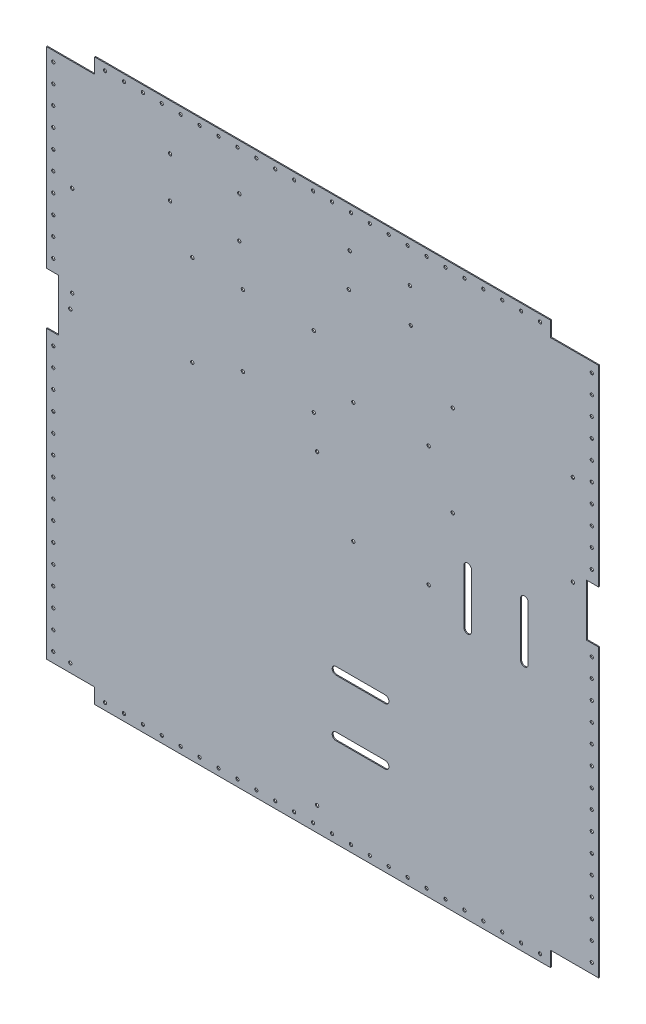
SolidWorks part; units mm, degrees
material "6061-T6 (SS)"
ref_plane "Front Plane" through (0, 0, 0) normal (0, 0, 1) x (1, 0, 0)
ref_plane "Top Plane" through (0, 0, 0) normal (0, 1, 0) x (1, 0, 0)
ref_plane "Right Plane" through (0, 0, 0) normal (1, 0, 0) x (0, 0, -1)
sketch "Sketch1" plane through (0, 0, 0) normal (0, 0, 1) x (1, 0, 0)
  line L0 (0, 374) -> (0, 577)
  line L1 (51, 0) -> (533, 0)
  line L2 (0, 16) -> (0, 319)
  line L3 (51, 593) -> (533, 593)
  line L4 (584, 16) -> (584, 319)
  line L7 (0, 16) -> (51, 16)
  line L8 (51, 0) -> (51, 16)
  line L11 (584, 16) -> (533, 16)
  line L12 (533, 0) -> (533, 16)
  line L13 (0, 319) -> (13, 319)
  line L15 (0, 374) -> (13, 374)
  line L16 (13, 319) -> (13, 374)
  line L17 (584, 319) -> (571, 319)
  line L19 (584, 374) -> (571, 374)
  line L20 (571, 319) -> (571, 374)
  line L23 (0, 577) -> (51, 577)
  line L24 (51, 593) -> (51, 577)
  line L27 (584, 577) -> (533, 577)
  line L28 (533, 593) -> (533, 577)
  line L29 (584, 374) -> (584, 577)
  point P25 (6.5, 319)
  point P26 (25.5, 577)
  dimension "D2" = 593
  dimension "D3" = 16
  dimension "D4" = 584
  dimension "D7" = 13
  dimension "D8" = 319
  dimension "D9" = 219
  dimension "D10" = 16
  dimension "D11" = 51
extrude "Boss-Extrude1" add sketch "Sketch1" along normal blind 1.016 contours L3 L28 L27 L29 L19 L20 L17 L4 L11 L12 L1 L8 L7 L2 L13 L16 L15 L0 L23 L24
sketch "Sketch2" plane through (0, 0, 1.016) normal (0, 0, 1) x (1, 0, 0)
  circle A0 centre (62, 585.825) radius 1.675
  circle A1 centre (82, 585.825) radius 1.675
  circle A2 centre (102, 585.825) radius 1.675
  circle A3 centre (122, 585.825) radius 1.675
  circle A4 centre (142, 585.825) radius 1.675
  circle A5 centre (162, 585.825) radius 1.675
  circle A6 centre (182, 585.825) radius 1.675
  circle A7 centre (202, 585.825) radius 1.675
  circle A8 centre (222, 585.825) radius 1.675
  circle A9 centre (242, 585.825) radius 1.675
  circle A10 centre (262, 585.825) radius 1.675
  circle A11 centre (282, 585.825) radius 1.675
  circle A12 centre (302, 585.825) radius 1.675
  circle A13 centre (322, 585.825) radius 1.675
  circle A14 centre (342, 585.825) radius 1.675
  circle A15 centre (362, 585.825) radius 1.675
  circle A16 centre (382, 585.825) radius 1.675
  circle A17 centre (402, 585.825) radius 1.675
  circle A18 centre (422, 585.825) radius 1.675
  circle A19 centre (442, 585.825) radius 1.675
  circle A20 centre (462, 585.825) radius 1.675
  circle A21 centre (482, 585.825) radius 1.675
  circle A22 centre (502, 585.825) radius 1.675
  circle A23 centre (522, 585.825) radius 1.675
  circle A24 centre (576.725, 566.5) radius 1.675
  circle A25 centre (576.725, 546.5) radius 1.675
  circle A26 centre (576.725, 526.5) radius 1.675
  circle A27 centre (576.725, 506.5) radius 1.675
  circle A28 centre (576.725, 486.5) radius 1.675
  circle A29 centre (576.725, 466.5) radius 1.675
  circle A30 centre (576.725, 446.5) radius 1.675
  circle A31 centre (576.725, 426.5) radius 1.675
  circle A32 centre (576.725, 406.5) radius 1.675
  circle A33 centre (576.725, 386.5) radius 1.675
  circle A34 centre (576.725, 306.5) radius 1.675
  circle A35 centre (576.725, 286.5) radius 1.675
  circle A36 centre (576.725, 266.5) radius 1.675
  circle A37 centre (576.725, 246.5) radius 1.675
  circle A38 centre (576.725, 226.5) radius 1.675
  circle A39 centre (576.725, 206.5) radius 1.675
  circle A40 centre (576.725, 186.5) radius 1.675
  circle A41 centre (576.725, 166.5) radius 1.675
  circle A42 centre (576.725, 146.5) radius 1.675
  circle A43 centre (576.725, 126.5) radius 1.675
  circle A44 centre (576.725, 106.5) radius 1.675
  circle A45 centre (576.725, 86.5) radius 1.675
  circle A46 centre (576.725, 66.5) radius 1.675
  circle A47 centre (576.725, 46.5) radius 1.675
  circle A48 centre (576.725, 26.5) radius 1.675
  circle A49 centre (522, 7.175) radius 1.675
  circle A50 centre (502, 7.175) radius 1.675
  circle A51 centre (482, 7.175) radius 1.675
  circle A52 centre (462, 7.175) radius 1.675
  circle A53 centre (442, 7.175) radius 1.675
  circle A54 centre (422, 7.175) radius 1.675
  circle A55 centre (402, 7.175) radius 1.675
  circle A56 centre (382, 7.175) radius 1.675
  circle A57 centre (362, 7.175) radius 1.675
  circle A58 centre (342, 7.175) radius 1.675
  circle A59 centre (322, 7.175) radius 1.675
  circle A60 centre (302, 7.175) radius 1.675
  circle A61 centre (282, 7.175) radius 1.675
  circle A62 centre (262, 7.175) radius 1.675
  circle A63 centre (242, 7.175) radius 1.675
  circle A64 centre (222, 7.175) radius 1.675
  circle A65 centre (202, 7.175) radius 1.675
  circle A66 centre (182, 7.175) radius 1.675
  circle A67 centre (162, 7.175) radius 1.675
  circle A68 centre (142, 7.175) radius 1.675
  circle A69 centre (122, 7.175) radius 1.675
  circle A70 centre (102, 7.175) radius 1.675
  circle A71 centre (62, 7.175) radius 1.675
  circle A72 centre (82, 7.175) radius 1.675
  circle A73 centre (7.275, 26.5) radius 1.675
  circle A74 centre (7.275, 46.5) radius 1.675
  circle A75 centre (7.275, 66.5) radius 1.675
  circle A76 centre (7.275, 86.5) radius 1.675
  circle A77 centre (7.275, 106.5) radius 1.675
  circle A78 centre (7.275, 126.5) radius 1.675
  circle A79 centre (7.275, 146.5) radius 1.675
  circle A80 centre (7.275, 166.5) radius 1.675
  circle A81 centre (7.275, 186.5) radius 1.675
  circle A82 centre (7.275, 206.5) radius 1.675
  circle A83 centre (7.275, 226.5) radius 1.675
  circle A84 centre (7.275, 246.5) radius 1.675
  circle A85 centre (7.275, 266.5) radius 1.675
  circle A86 centre (7.275, 286.5) radius 1.675
  circle A87 centre (7.275, 306.5) radius 1.675
  circle A88 centre (7.275, 386.5) radius 1.675
  circle A89 centre (7.275, 406.5) radius 1.675
  circle A90 centre (7.275, 426.5) radius 1.675
  circle A91 centre (7.275, 446.5) radius 1.675
  circle A92 centre (7.275, 466.5) radius 1.675
  circle A93 centre (7.275, 486.5) radius 1.675
  circle A94 centre (7.275, 506.5) radius 1.675
  circle A95 centre (7.275, 526.5) radius 1.675
  circle A96 centre (7.275, 546.5) radius 1.675
  circle A97 centre (7.275, 566.5) radius 1.675
  dimension "D1" = 3.35
extrude "Cut-Extrude1" cut sketch "Sketch2" against normal through all
sketch "Sketch4" plane through (0, 0, 1.016) normal (0, 0, 1) x (1, 0, 0)
  line L20 (51, 593) -> (51, 577)
  line L21 (51, 577) -> (0, 577)
  line L22 (0, 577) -> (0, 374)
  line L23 (0, 374) -> (13, 374)
  line L24 (13, 374) -> (13, 319)
  line L25 (13, 319) -> (0, 319)
  line L26 (0, 319) -> (0, 16)
  line L27 (0, 16) -> (51, 16)
  line L28 (51, 16) -> (51, 0)
  line L29 (51, 0) -> (533, 0)
  line L30 (533, 0) -> (533, 16)
  line L31 (533, 16) -> (584, 16)
  line L32 (584, 16) -> (584, 319)
  line L33 (584, 319) -> (571, 319)
  line L34 (571, 319) -> (571, 374)
  line L35 (571, 374) -> (584, 374)
  line L36 (584, 374) -> (584, 577)
  line L37 (584, 577) -> (533, 577)
  line L38 (533, 577) -> (533, 593)
  line L39 (533, 593) -> (51, 593)
  line L40 (51, 593) -> (51, 577)
  line L41 (51, 577) -> (0, 577)
  line L42 (0, 577) -> (0, 374)
  line L43 (0, 374) -> (13, 374)
  line L44 (13, 374) -> (13, 319)
  line L45 (13, 319) -> (0, 319)
  line L46 (0, 319) -> (0, 16)
  line L47 (0, 16) -> (51, 16)
  line L48 (51, 16) -> (51, 0)
  line L49 (51, 0) -> (533, 0)
  line L50 (533, 0) -> (533, 16)
  line L51 (533, 16) -> (584, 16)
  line L52 (584, 16) -> (584, 319)
  line L53 (584, 319) -> (571, 319)
  line L54 (571, 319) -> (571, 374)
  line L55 (571, 374) -> (584, 374)
  line L56 (584, 374) -> (584, 577)
  line L57 (584, 577) -> (533, 577)
  line L58 (533, 577) -> (533, 593)
  line L59 (533, 593) -> (51, 593)
  dimension "D1" = 0
sketch "Sketch8" plane through (0, 0, 1.016) normal (0, 0, 1) x (1, 0, 0)
  circle A0 centre (130.7804, 544.2217) radius 1.75
  circle A1 centre (203.9804, 544.2217) radius 1.75
  circle A2 centre (130.7804, 501.0217) radius 1.75
  circle A3 centre (203.9804, 501.0217) radius 1.75
  circle A4 centre (320.775, 550.325) radius 1.75
  circle A5 centre (319.775, 514.325) radius 1.75
  circle A6 centre (385.375, 514.325) radius 1.75
  circle A7 centre (384.375, 550.325) radius 1.75
  circle A8 centre (429.725, 460.825) radius 1.75
  circle A9 centre (556.725, 460.825) radius 1.75
  circle A10 centre (556.725, 364.825) radius 1.75
  circle A11 centre (429.725, 364.825) radius 1.75
  circle A12 centre (324.55, 413.325) radius 1.75
  circle A13 centre (404.225, 413.325) radius 1.75
  circle A14 centre (324.55, 286.025) radius 1.75
  circle A15 centre (404.225, 286.025) radius 1.75
  circle A16 centre (286.275, 25.175) radius 1.75
  circle A17 centre (25.275, 25.175) radius 1.75
  circle A18 centre (25.275, 349.175) radius 1.75
  circle A19 centre (286.275, 349.175) radius 1.75
  circle A20 centre (154.275, 460.825) radius 1.75
  circle A21 centre (27.275, 460.825) radius 1.75
  circle A22 centre (27.275, 364.825) radius 1.75
  circle A23 centre (154.275, 364.825) radius 1.75
  circle A24 centre (207.775, 458.325) radius 1.75
  circle A25 centre (207.775, 383.325) radius 1.75
  circle A26 centre (282.775, 458.325) radius 1.75
  circle A27 centre (282.775, 383.325) radius 1.75
  dimension "D1" = 3.5
extrude "Cut-Extrude2" cut sketch "Sketch8" against normal through all
sketch "Sketch9" plane through (0, 0, 1.016) normal (0, 0, 1) x (1, 0, 0)
  line L0 (505.475, 265.675) -> (505.475, 322.675) construction
  line L1 (501.475, 265.675) -> (501.475, 322.675)
  line L2 (509.475, 265.675) -> (509.475, 322.675)
  line L3 (445.475, 265.675) -> (445.475, 322.675) construction
  line L4 (441.475, 265.675) -> (441.475, 322.675)
  line L5 (449.475, 265.675) -> (449.475, 322.675)
  line L6 (358.225, 158.425) -> (306.225, 158.425) construction
  line L7 (358.225, 154.425) -> (306.225, 154.425)
  line L8 (358.225, 162.425) -> (306.225, 162.425)
  line L9 (306.225, 98.425) -> (358.225, 98.425) construction
  line L10 (306.225, 102.425) -> (358.225, 102.425)
  line L11 (306.225, 94.425) -> (358.225, 94.425)
  arc A0 (501.475, 265.675) -> (509.475, 265.675) centre (505.475, 265.675) ccw
  arc A1 (509.475, 322.675) -> (501.475, 322.675) centre (505.475, 322.675) ccw
  arc A2 (441.475, 265.675) -> (449.475, 265.675) centre (445.475, 265.675) ccw
  arc A3 (449.475, 322.675) -> (441.475, 322.675) centre (445.475, 322.675) ccw
  arc A4 (358.225, 154.425) -> (358.225, 162.425) centre (358.225, 158.425) ccw
  arc A5 (306.225, 162.425) -> (306.225, 154.425) centre (306.225, 158.425) ccw
  arc A6 (306.225, 102.425) -> (306.225, 94.425) centre (306.225, 98.425) ccw
  arc A7 (358.225, 94.425) -> (358.225, 102.425) centre (358.225, 98.425) ccw
  point P4 (505.475, 294.175)
  point P9 (445.475, 294.175)
  point P18 (332.225, 158.425)
  point P27 (332.225, 98.425)
  dimension "D1" = 4
  dimension "D2" = 4
  dimension "D3" = 4
  dimension "D4" = 4
extrude "Cut-Extrude3" cut sketch "Sketch9" against normal through all
